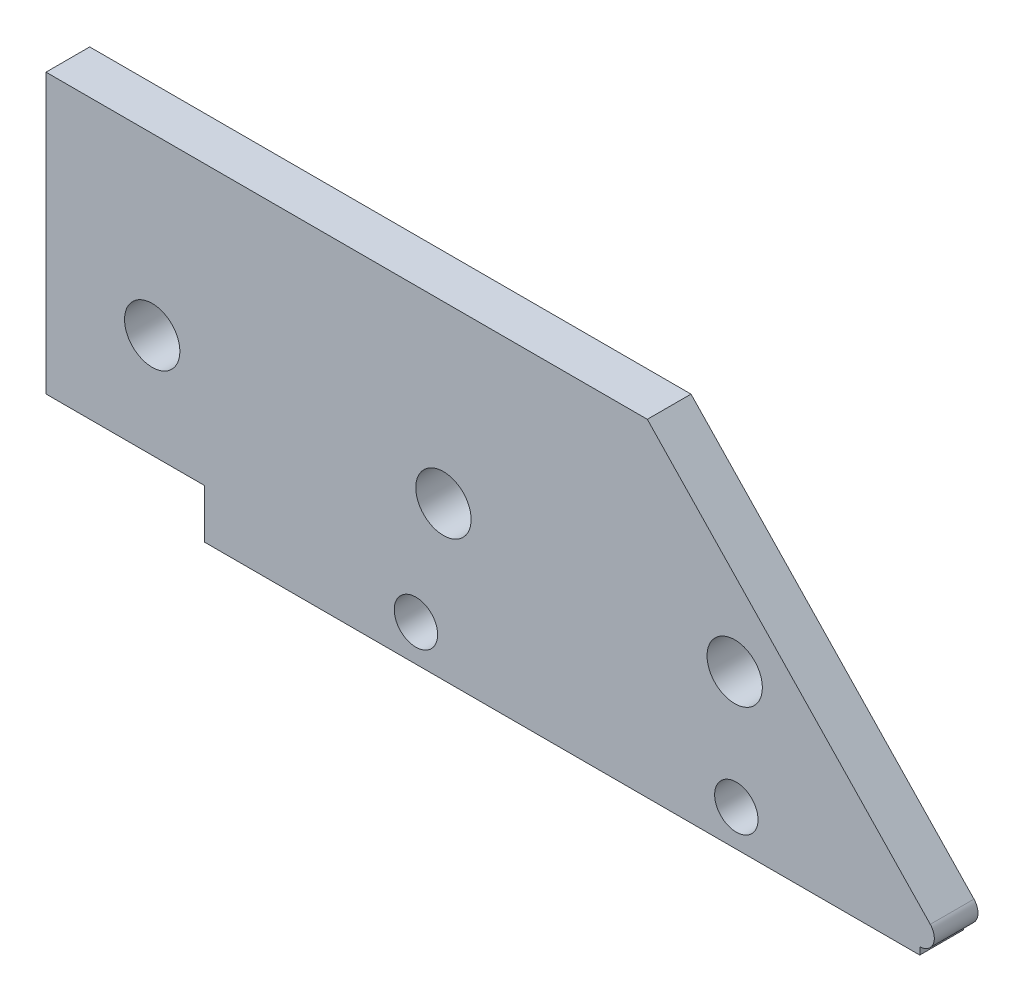
SolidWorks part; units mm, degrees
material "Резина"
ref_plane "Спереди" through (0, 0, 0) normal (0, 0, 1) x (1, 0, 0)
ref_plane "Сверху" through (0, 0, 0) normal (0, 1, 0) x (1, 0, 0)
ref_plane "Справа" through (0, 0, 0) normal (1, 0, 0) x (0, 0, -1)
sketch "Эскиз1" plane through (0, 0, 0) normal (0, 0, 1) x (1, 0, 0)
  line L0 (45.3014, 22.3839) -> (45.3014, -1.4526)
  line L5 (53.6615, 0.375) -> (105.3014, 0.375)
  line L6 (106.0241, 2.0662) -> (86.5935, 22.3839)
  line L7 (86.5935, 22.3839) -> (13.4172, 22.3839)
  line L8 (0, -10) -> (53, 0)
  line L9 (53, 0) -> (53.6615, 0.375)
  line L10 (53.6615, 0.375) -> (105.3014, 0.375)
  line L11 (106.0241, 2.0662) -> (86.5935, 22.3839)
  line L12 (86.5935, 22.3839) -> (45.3014, 22.3839)
  line L13 (45.3014, -1.4526) -> (53, 0)
  line L14 (53, 0) -> (53.6615, 0.375)
  arc A3 (105.3014, 0.375) -> (106.0241, 2.0662) centre (105.3014, 1.375) ccw
  arc A4 (13.4172, 22.3839) -> (-10, 0) centre (13.4172, -1.0571) ccw
  arc A5 (-10, 0) -> (0, -10) centre (0, 0) ccw
  arc A6 (105.3014, 0.375) -> (106.0241, 2.0662) centre (105.3014, 1.375) ccw
  dimension "D2" = 60
  dimension "D1" = 0
extrude "Бобышка-Вытянуть1" add sketch "Эскиз1" along normal blind 3
sketch "Эскиз2" plane through (0, 0, 3) normal (0, 0, 1) x (1, 0, 0)
  line L0 (45.3014, 3.2425) -> (56.1877, 3.2425)
  line L1 (45.3014, 22.3839) -> (45.3014, -1.4526) construction
  line L2 (56.1877, 3.2425) -> (56.1877, -5.4665)
  line L3 (56.1877, -5.4665) -> (45.3014, -5.4665)
  line L4 (45.3014, -22.5089) -> (45.3014, 1.3276) construction
  line L5 (45.3014, -5.4665) -> (45.3014, 3.2425)
extrude "Вырез-Вытянуть1" cut sketch "Эскиз2" against normal through all both and the other way through all
sketch "Эскиз3" plane through (0, 0, 3) normal (0, 0, 1) x (1, 0, 0)
  circle A0 centre (52.5935, 10.375) radius 1.9
  circle A1 centre (52.5935, 10.375) radius 1.25
  circle A2 centre (52.5935, 10.375) radius 1.25 construction
  circle A3 centre (72.5935, 10.375) radius 1.25
  circle A4 centre (72.5935, 10.375) radius 1.25 construction
  circle A5 centre (92.5935, 10.375) radius 1.25
  circle A6 centre (92.5935, 10.375) radius 1.25 construction
  circle A7 centre (72.5935, 10.375) radius 1.9
  circle A8 centre (92.5935, 10.375) radius 1.9
  dimension "D1" = 0
  dimension "D2" = 0
  dimension "D3" = 0
  dimension "D4" = 0.65
extrude "Вырез-Вытянуть2" cut sketch "Эскиз3" against normal through all both and the other way through all
sketch "Эскиз4" plane through (0, 0, 3) normal (0, 0, 1) x (1, 0, 0)
  circle A0 centre (92.7052, 2.375) radius 1.25 construction
  circle A1 centre (92.7052, 2.375) radius 1.25 construction
  circle A2 centre (70.7052, 2.375) radius 1.25 construction
  circle A3 centre (70.7052, 2.375) radius 1.25 construction
  circle A4 centre (92.7052, 2.375) radius 1.49
  circle A5 centre (70.7052, 2.375) radius 1.49
  dimension "D1" = 0.24
extrude "Вырез-Вытянуть3" cut sketch "Эскиз4" against normal through all both and the other way through all
sketch "Эскиз5" plane through (0, 0, 3) normal (0, 0, 1) x (1, 0, 0)
  line L0 (56.1877, 0.375) -> (56.1877, 3.2425) construction
  line L1 (105.3014, 0.375) -> (56.1877, 0.375)
  line L2 (105.3014, 0.375) -> (105.3014, -0.125)
  line L3 (105.3014, -0.125) -> (56.1877, -0.125)
  line L4 (56.1877, 0.375) -> (56.1877, -0.125)
  dimension "D1" = 0.5
extrude "Бобышка-Вытянуть2" add sketch "Эскиз5" against normal up to surface (3 mm away) up to face at (72.1952, 2.375, 0)
